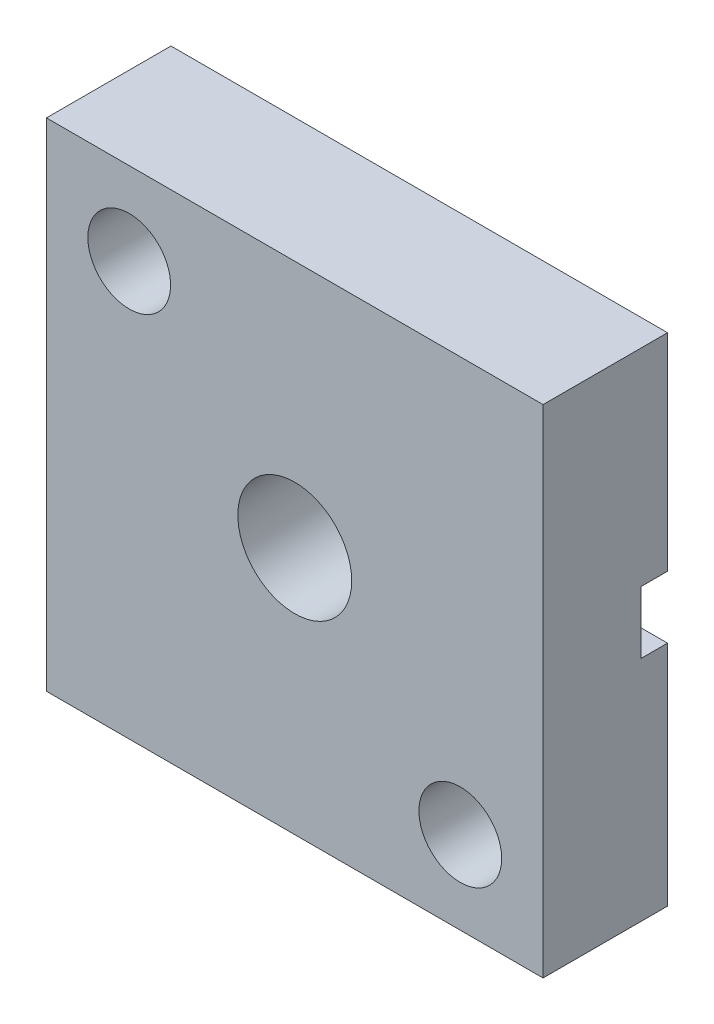
SolidWorks part; units mm, degrees
ref_plane "Front Plane" through (0, 0, 0) normal (0, 0, 1) x (1, 0, 0)
ref_plane "Top Plane" through (0, 0, 0) normal (0, 1, 0) x (1, 0, 0)
ref_plane "Right Plane" through (0, 0, 0) normal (1, 0, 0) x (0, 0, -1)
sketch "Sketch1" plane through (0, 0, 0) normal (0, 0, 1) x (1, 0, 0)
  line L1 (-141.383, -95.2475) -> (-122.333, -95.2475)
  line L2 (-141.383, -95.2475) -> (-141.383, -76.1975)
  line L3 (-141.383, -76.1975) -> (-122.333, -76.1975)
  line L4 (-122.333, -95.2475) -> (-122.333, -76.1975)
  dimension "D1" = 19.05
  dimension "D2" = 19.05
extrude "Extrude1" add sketch "Sketch1" along normal blind 4.7752
sketch "Sketch2" plane through (0, 0, 4.7752) normal (0, 0, 1) x (1, 0, 0)
  line L0 (-122.333, -76.1975) -> (-141.383, -76.1975) construction
  line L1 (-141.383, -76.1975) -> (-141.383, -95.2475) construction
  line L2 (-141.383, -95.2475) -> (-122.333, -95.2475) construction
  line L3 (-122.333, -95.2475) -> (-122.333, -76.1975) construction
  circle A0 centre (-131.858, -85.7225) radius 2.1844
  circle A1 centre (-125.508, -92.0725) radius 1.5875
  circle A2 centre (-138.208, -79.3725) radius 1.5875
  dimension "D1" = 4.3688
  dimension "D2" = 3.175
  dimension "D3" = 3.175
  dimension "D4" = 3.175
  dimension "D5" = 3.175
  dimension "D6" = 3.175
extrude "Extrude2" cut sketch "Sketch2" against normal through all
sketch "Sketch4" plane through (-141.383, 0, 0) normal (-1, 0, 0) x (0, 0, 1)
  line L0 (0, -76.1975) -> (0, -95.2475) construction
  line L1 (0, -76.1975) -> (0, -95.2475) construction
  line L2 (0, -85.3161) -> (-14.654, -85.3161) construction
  line L10 (0, -84.1223) -> (0, -86.5099)
  line L11 (0, -86.5099) -> (1.016, -86.5099)
  line L12 (0, -84.1223) -> (1.016, -84.1223)
  line L13 (1.016, -84.1223) -> (1.016, -86.5099)
  line L14 (1.016, -76.1975) -> (1.016, -95.2475) construction
  dimension "D1" = 2.3876
  dimension "D3" = 1.016
extrude "Extrude3" cut sketch "Sketch4" against normal through all
